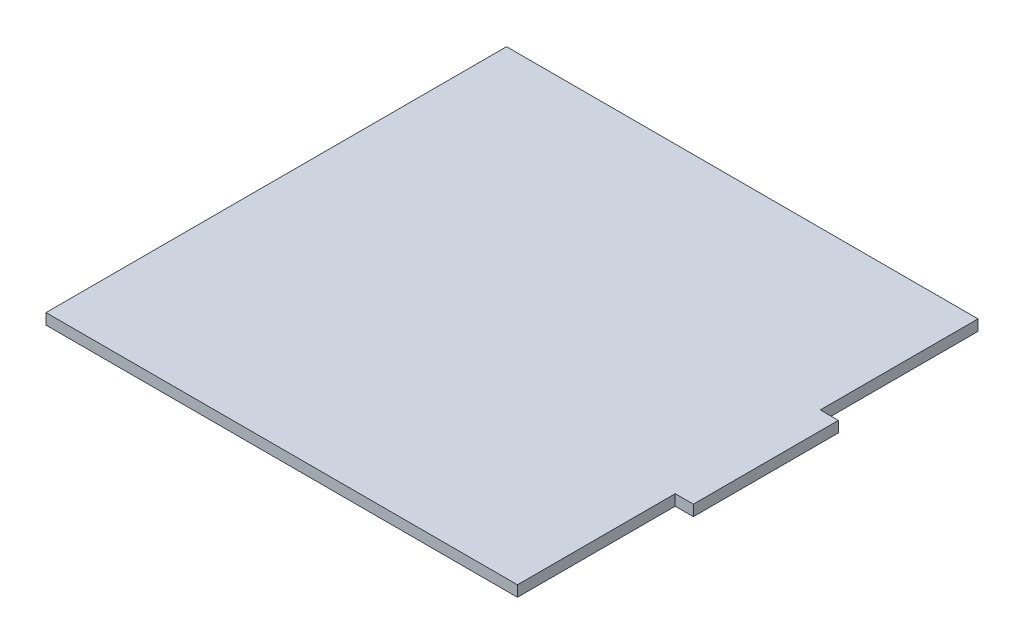
SolidWorks part; units mm, degrees
ref_plane "Front Plane" through (0, 0, 0) normal (0, 0, 1) x (1, 0, 0)
ref_plane "Top Plane" through (0, 0, 0) normal (0, 1, 0) x (1, 0, 0)
ref_plane "Right Plane" through (0, 0, 0) normal (1, 0, 0) x (0, 0, -1)
sketch "Sketch1" plane through (0, 0, 0) normal (0, 1, 0) x (1, 0, 0)
  line L0 (65, 20) -> (70, 20)
  line L1 (-65, 63.5) -> (65, 63.5)
  line L2 (-65, 63.5) -> (-65, -63.5)
  line L3 (-65, -63.5) -> (65, -63.5)
  line L4 (65, 63.5) -> (65, 20)
  line L5 (-65, 63.5) -> (65, -63.5) construction
  line L6 (-65, -63.5) -> (65, 63.5) construction
  line L7 (70, 20) -> (70, -20)
  line L8 (70, -20) -> (65, -20)
  line L9 (70, 0) -> (-65, 0) construction
  line L10 (65, -20) -> (65, -63.5)
  point P0 (0, 0)
  dimension "D1" = 130
  dimension "D2" = 127
  dimension "D3" = 40
  dimension "D4" = 5
extrude "Boss-Extrude1" add sketch "Sketch1" along normal blind 3
